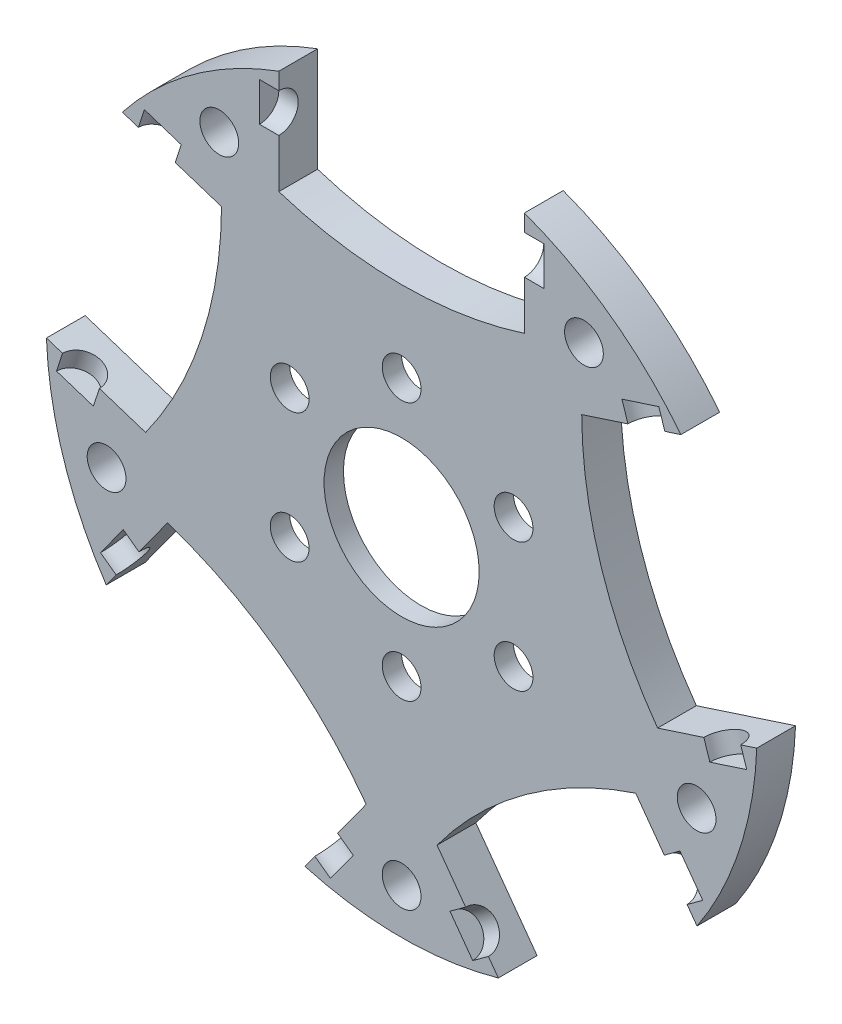
SolidWorks part; units mm, degrees
ref_plane "Front Plane" through (0, 0, 0) normal (0, 0, 1) x (1, 0, 0)
ref_plane "Top Plane" through (0, 0, 0) normal (0, 1, 0) x (1, 0, 0)
ref_plane "Right Plane" through (0, 0, 0) normal (1, 0, 0) x (0, 0, -1)
sketch "Sketch1" plane through (0, 0, 0) normal (0, 0, 1) x (1, 0, 0)
  line L0 (-9.5, 25.807) -> (-9.5, 17.7375)
  line L1 (9.5, 25.807) -> (9.5, 17.7375)
  line L2 (21.6082, 17.0098) -> (13.9337, 14.5162)
  line L3 (27.4796, -1.0602) -> (19.805, -3.5538)
  line L4 (22.8546, -15.2943) -> (18.1115, -8.766)
  line L5 (7.4833, -26.4622) -> (2.7402, -19.9339)
  line L6 (-7.4833, -26.4622) -> (-2.7402, -19.9339)
  line L7 (-22.8546, -15.2943) -> (-18.1115, -8.766)
  line L8 (-27.4796, -1.0602) -> (-19.805, -3.5538)
  line L9 (-21.6082, 17.0098) -> (-13.9337, 14.5162)
  arc A0 (-9.5, 25.807) -> (-21.6082, 17.0098) centre (0, 0) ccw
  circle A1 centre (0, 0) radius 16.25 construction
  arc A2 (-9.5, 17.7375) -> (9.5, 17.7375) centre (0, 47.33) ccw
  arc A3 (13.9337, 14.5162) -> (19.805, -3.5538) centre (45.0135, 14.6258) ccw
  arc A4 (18.1115, -8.766) -> (2.7402, -19.9339) centre (27.8199, -38.2908) ccw
  arc A5 (-2.7402, -19.9339) -> (-18.1115, -8.766) centre (-27.8199, -38.2908) ccw
  arc A6 (-19.805, -3.5538) -> (-13.9337, 14.5162) centre (-45.0135, 14.6258) ccw
  arc A7 (-27.4796, -1.0602) -> (-22.8546, -15.2943) centre (0, 0) ccw
  arc A8 (-7.4833, -26.4622) -> (7.4833, -26.4622) centre (0, 0) ccw
  arc A9 (22.8546, -15.2943) -> (27.4796, -1.0602) centre (0, 0) ccw
  arc A10 (21.6082, 17.0098) -> (9.5, 25.807) centre (0, 0) ccw
  dimension "D1" = 55
  dimension "D4" = 32.5
  dimension "D5" = 31.08
  dimension "D2" = 19
  dimension "D3" = 9.5
  dimension "D6" = 5
extrude "Boss-Extrude1" add sketch "Sketch1" along normal blind 3
sketch "Sketch2" plane through (0, 0, 3) normal (0, 0, 1) x (1, 0, 0)
  line L0 (0, 0) -> (16.1641, 22.248) construction
  circle A0 centre (0, 0) radius 10 construction
  circle A1 centre (0, 10) radius 1.5
  circle A7 centre (-8.6603, 5) radius 1.5
  circle A8 centre (-8.6603, -5) radius 1.5
  circle A9 centre (0, -10) radius 1.5
  circle A10 centre (8.6603, -5) radius 1.5
  circle A11 centre (8.6603, 5) radius 1.5
  circle A12 centre (0, 0) radius 6
  arc A13 (21.6082, 17.0098) -> (9.5, 25.807) centre (0, 0) ccw construction
  circle A14 centre (14.1068, 19.4164) radius 1.5
  circle A20 centre (22.8254, -7.4164) radius 1.5
  circle A21 centre (0, -24) radius 1.5
  circle A22 centre (-22.8254, -7.4164) radius 1.5
  circle A23 centre (-14.1068, 19.4164) radius 1.5
  dimension "D1" = 20
  dimension "D2" = 3
  dimension "D4" = 12
  dimension "D5" = 3
  dimension "D6" = 24
  dimension "D3" = 6
  dimension "D7" = 5
extrude "Cut-Extrude1" cut sketch "Sketch2" against normal blind 3
sketch "Sketch5" plane through (0, 0, 3) normal (0, 0, 1) x (1, 0, 0)
  line L0 (0, -28.4643) -> (0, 26.3222) construction
  line L1 (11, 23) -> (-11, 23) construction
  line L2 (-11, 23) -> (-11, 24.5)
  line L3 (-11, 24.5) -> (11, 24.5)
  line L4 (11, 24.5) -> (11, 23)
  line L5 (-11, 23) -> (11, 23)
  point P6 (0, 23)
  dimension "D1" = 22
  dimension "D2" = 23
  dimension "D3" = 3
revolve "Cut-Revolve1" cut sketch "Sketch5" angle 360 about L5
pattern_circular "CirPattern1" count 5 over 360 about axis through (0, 0, 0) along (0, 0, 1) of "Cut-Revolve1"
sketch "Sketch6" plane through (0, 0, 0) normal (0, 0, -1) x (-1, 0, 0)
  circle A0 centre (0, 0) radius 14
  dimension "D1" = 28
extrude "Cut-Extrude2" cut sketch "Sketch6" against normal blind 1.5
